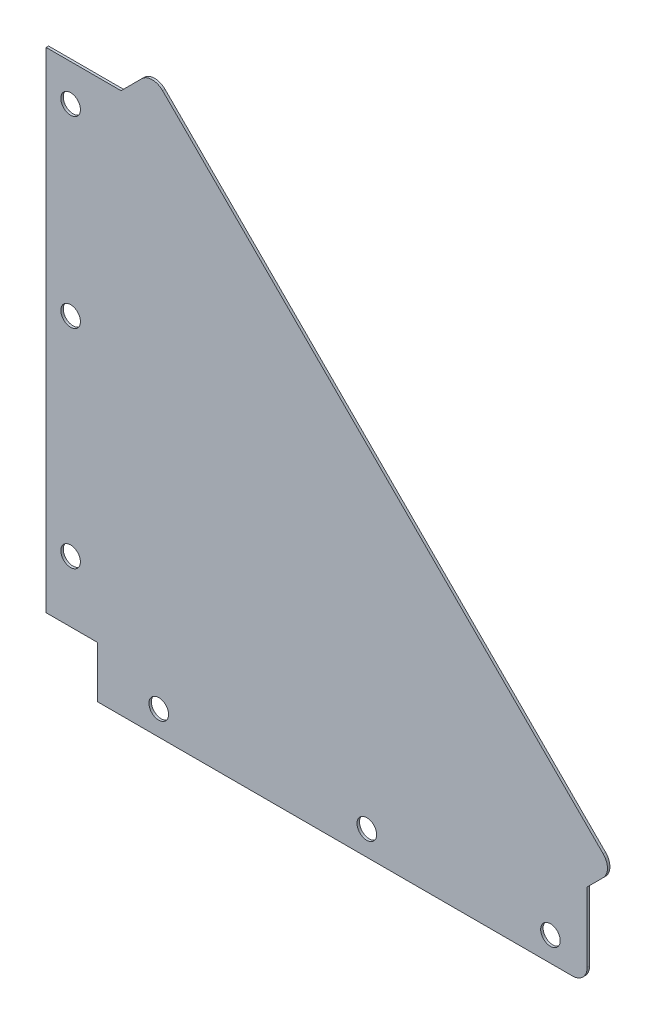
SolidWorks part; units mm, degrees
ref_plane "前基準面" through (0, 0, 0) normal (0, 0, 1) x (1, 0, 0)
ref_plane "上基準面" through (0, 0, 0) normal (0, 1, 0) x (1, 0, 0)
ref_plane "右基準面" through (0, 0, 0) normal (1, 0, 0) x (0, 0, -1)
sketch "草圖1" plane through (0, 0, 0) normal (0, 0, 1) x (1, 0, 0)
  line L0 (0, 21) -> (21, 21)
  line L1 (21, 21) -> (21, 0)
  line L2 (21, 0) -> (215, 0)
  line L3 (221, 6) -> (221, 34.5)
  line L4 (221, 34.5) -> (227.5355, 41.0355)
  line L5 (227.5355, 49.5208) -> (47.5711, 229.4853)
  line L6 (39.0858, 229.4853) -> (30.6005, 221)
  line L7 (30.6005, 221) -> (0, 221)
  line L8 (0, 221) -> (0, 21)
  line L9 (224, 37.5) -> (35.5503, 225.9497) construction
  line L10 (221, 21) -> (-93.028, 21) construction
  line L11 (10, 234.6597) -> (10, -33.5206) construction
  arc A0 (215, 0) -> (221, 6) centre (215, 6) ccw
  arc A1 (47.5711, 229.4853) -> (39.0858, 229.4853) centre (43.3284, 225.2426) ccw
  arc A2 (227.5355, 41.0355) -> (227.5355, 49.5208) centre (223.2929, 45.2782) ccw
  circle A3 centre (10, 206) radius 4
  circle A4 centre (10, 46) radius 4
  circle A5 centre (10, 131) radius 4
  circle A6 centre (46, 10) radius 4
  circle A7 centre (131, 10) radius 4
  circle A8 centre (206, 10) radius 4
  point P16 (221, 0)
  dimension "D11" = 6
  dimension "D14" = 15
  dimension "D15" = 75
  dimension "D16" = 85
  dimension "D17" = 15
  dimension "D18" = 75
  dimension "D19" = 85
  dimension "D20" = 8
  dimension "D1" = 21
  dimension "D2" = 21
  dimension "D3" = 200
  dimension "D4" = 200
  dimension "D5" = 135
  dimension "D6" = 34.5
  dimension "D7" = 11
  dimension "D8" = 21
  dimension "D9" = 16.5
  dimension "D10" = 7
  dimension "D12" = 10
  dimension "D13" = 10
extrude "填料-伸長1" add sketch "草圖1" along normal blind 1 contours L5 A1 L6 L7 L8 L0 L1 L2 A0 L3 L4 A2
